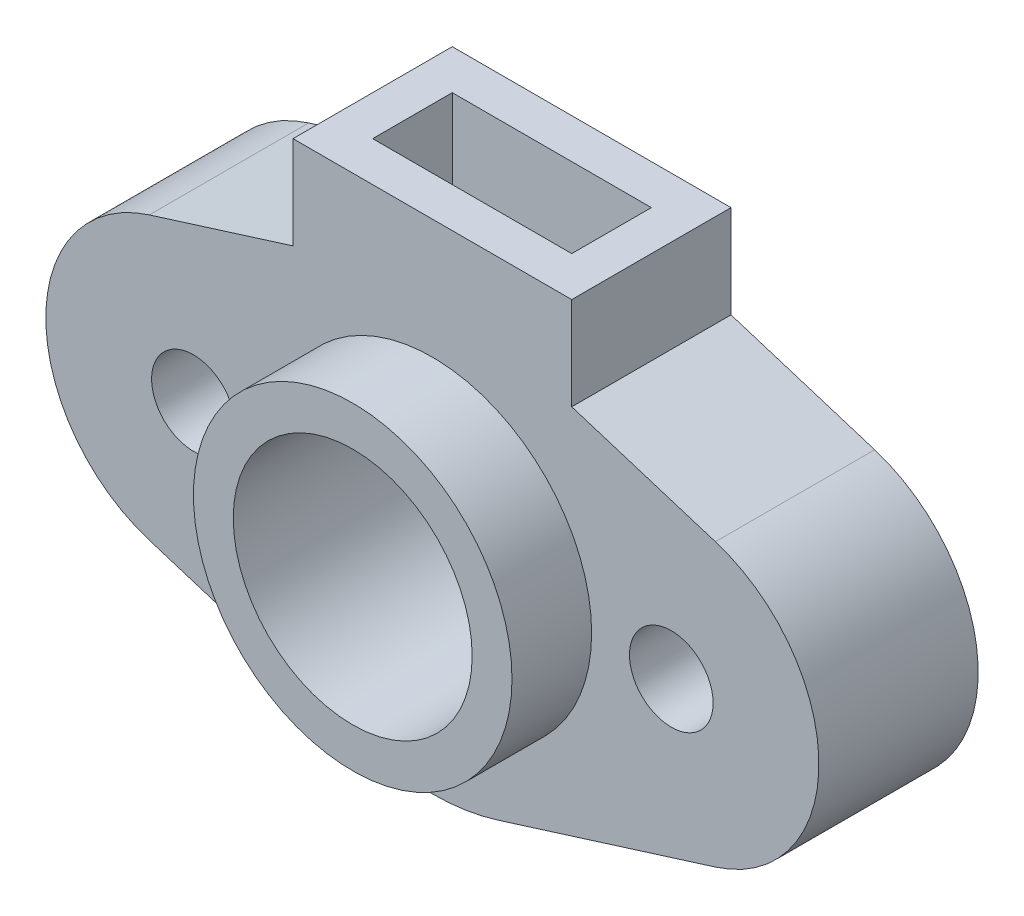
SolidWorks part; units mm, degrees
ref_plane "Ön Düzlem" through (0, 0, 0) normal (0, 0, 1) x (1, 0, 0)
ref_plane "Üst Düzlem" through (0, 0, 0) normal (0, 1, 0) x (1, 0, 0)
ref_plane "Sağ Düzlem" through (0, 0, 0) normal (1, 0, 0) x (0, 0, -1)
sketch "Çizim1" plane through (0, 0, 0) normal (0, 0, 1) x (1, 0, 0)
  line L0 (0, 0) -> (176.2698, 0) construction
  line L1 (0, 0) -> (0, 101.337) construction
  line L2 (71.0779, 35.3755) -> (16.4363, 52.4866)
  line L3 (71.0779, -35.3755) -> (16.4363, -52.4866)
  line L4 (-71.0779, -35.3755) -> (-16.4363, -52.4866)
  line L5 (-71.0779, 35.3755) -> (-16.4363, 52.4866)
  circle A0 centre (0, 0) radius 30
  circle A1 centre (0, 0) radius 40
  arc A2 (16.4363, 52.4866) -> (-16.4363, 52.4866) centre (0, 0) ccw
  arc A3 (71.0779, -35.3755) -> (71.0779, 35.3755) centre (60, 0) ccw
  circle A4 centre (60, 0) radius 10.5
  circle A5 centre (-60, 0) radius 10.5
  arc A6 (-71.0779, -35.3755) -> (-71.0779, 35.3755) centre (-60, 0) cw
  arc A8 (-16.4363, -52.4866) -> (16.4363, -52.4866) centre (0, 0) ccw
  dimension "D1" = 60
  dimension "D2" = 80
  dimension "D3" = 110
  dimension "D4" = 21
  dimension "D5" = 120
extrude "Yükseklik-Ekstrüzyon1" add sketch "Çizim1" along normal mid plane 40 contours L4 A8 L3 A3 L2 A2 L5 A6 A5 A4 A1 | A1 A0
sketch "Çizim2" plane through (0, 0, 20) normal (0, 0, 1) x (1, 0, 0)
  line L0 (-71.0779, -35.3755) -> (-16.4363, -52.4866) construction
  line L1 (71.0779, -35.3755) -> (16.4363, -52.4866) construction
  line L2 (71.0779, 35.3755) -> (16.4363, 52.4866) construction
  line L3 (-71.0779, 35.3755) -> (-16.4363, 52.4866) construction
  line L4 (-71.0779, -35.3755) -> (-16.4363, -52.4866)
  line L5 (71.0779, -35.3755) -> (16.4363, -52.4866)
  line L6 (71.0779, 35.3755) -> (16.4363, 52.4866)
  line L7 (-71.0779, 35.3755) -> (-16.4363, 52.4866)
  circle A0 centre (60, 0) radius 10.5 construction
  circle A1 centre (-60, 0) radius 10.5 construction
  arc A2 (-71.0779, 35.3755) -> (-71.0779, -35.3755) centre (-60, 0) ccw construction
  arc A3 (-16.4363, -52.4866) -> (16.4363, -52.4866) centre (0, 0) ccw construction
  arc A4 (71.0779, -35.3755) -> (71.0779, 35.3755) centre (60, 0) ccw construction
  arc A5 (16.4363, 52.4866) -> (-16.4363, 52.4866) centre (0, 0) ccw construction
  circle A6 centre (60, 0) radius 10.5
  circle A7 centre (-60, 0) radius 10.5
  arc A8 (-71.0779, 35.3755) -> (-71.0779, -35.3755) centre (-60, 0) ccw
  arc A9 (-16.4363, -52.4866) -> (16.4363, -52.4866) centre (0, 0) ccw
  arc A10 (71.0779, -35.3755) -> (71.0779, 35.3755) centre (60, 0) ccw
  arc A11 (16.4363, 52.4866) -> (-16.4363, 52.4866) centre (0, 0) ccw
  circle A12 centre (0, 0) radius 30 construction
  circle A13 centre (0, 0) radius 30
sketch "Çizim3" plane through (0, 0, 20) normal (0, 0, 1) x (1, 0, 0)
  circle A0 centre (0, 0) radius 40
  circle A1 centre (0, 0) radius 30 construction
  circle A2 centre (0, 0) radius 30
  circle A3 centre (0, 0) radius 30
  circle M13 centre (0, 0) radius 30
  dimension "D1" = 80
extrude "Yükseklik-Ekstrüzyon2" add sketch "Çizim3" along normal blind 20 contours A0 M13
sketch "Çizim4" plane through (0, 0, 20) normal (0, 0, 1) x (1, 0, 0)
  line L0 (-35, 30) -> (-35, 70)
  line L1 (-35, 30) -> (35, 30)
  line L3 (-35, 70) -> (35, 70)
  line L4 (35, 30) -> (35, 70)
  point P4 (0, 0)
  point P6 (35, 41.9463)
  point P7 (0, 70)
  point P8 (0, 0)
  point P9 (0, 30)
  dimension "D2" = 70
extrude "Yükseklik-Ekstrüzyon3" add sketch "Çizim4" against normal up to surface (40 mm away) up to face at (-49.5, 0, -20)
sketch "Çizim6" plane through (0, 70, 0) normal (0, 1, 0) x (1, 0, 0)
  line L0 (-35, 20) -> (35, 20) construction
  line L1 (-25, 10) -> (25, 10)
  line L2 (-25, 10) -> (-25, -10)
  line L3 (-25, -10) -> (25, -10)
  line L4 (25, 10) -> (25, -10)
  line L5 (35, -20) -> (-35, -20) construction
  line L6 (35, 20) -> (35, -20) construction
  point P8 (0, 10)
  dimension "D1" = 10
  dimension "D2" = 10
  dimension "D3" = 10
extrude "Kes-Ekstrüzyon4" cut sketch "Çizim6" against normal blind 30
sketch "Çizim8" plane through (0, 40, 0) normal (0, 1, 0) x (1, 0, 0)
  circle A0 centre (0, 0) radius 5
  dimension "D1" = 10
extrude "Kes-Ekstrüzyon5" cut sketch "Çizim8" against normal through all
